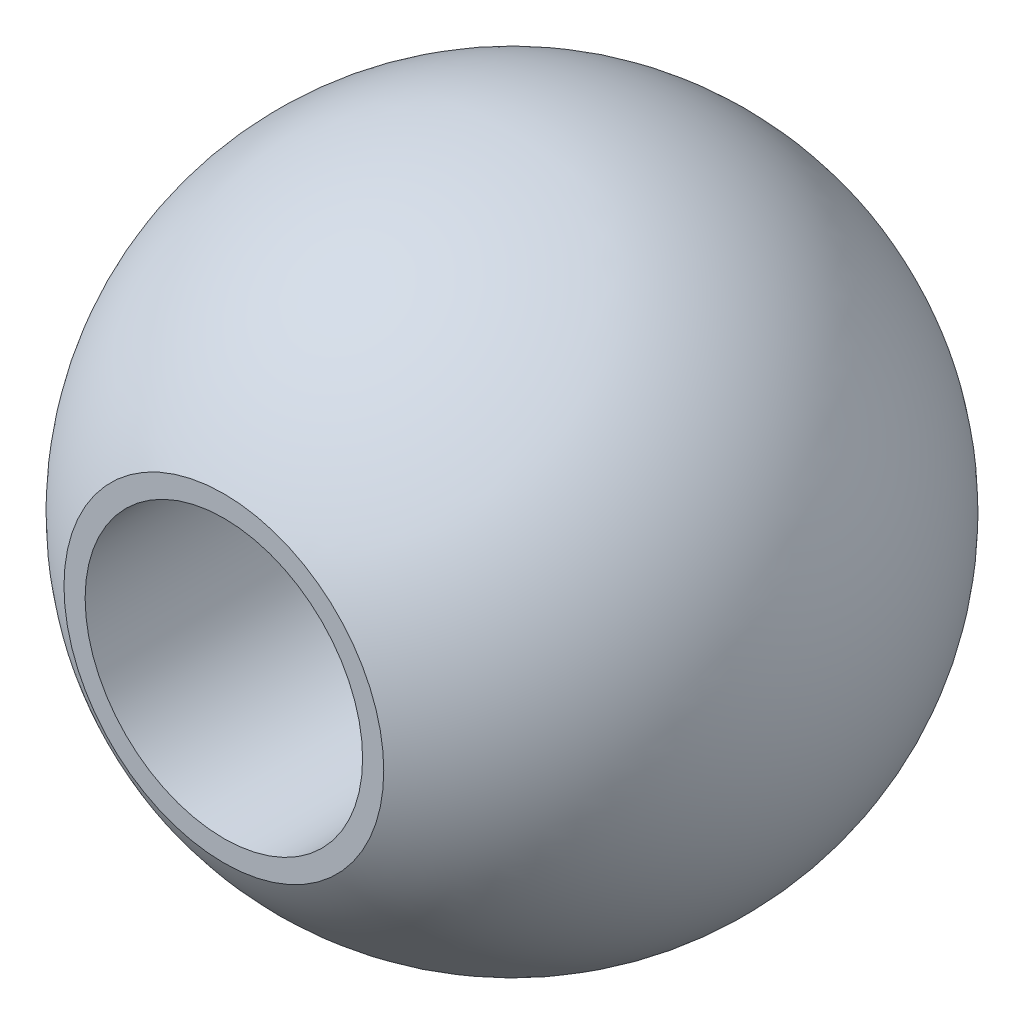
SolidWorks part; units mm, degrees
ref_plane "Front Plane" through (0, 0, 0) normal (0, 0, 1) x (1, 0, 0)
ref_plane "Top Plane" through (0, 0, 0) normal (0, 1, 0) x (1, 0, 0)
ref_plane "Right Plane" through (0, 0, 0) normal (1, 0, 0) x (0, 0, -1)
sketch "Sketch1" plane through (0, 0, 0) normal (0, 0, 1) x (1, 0, 0)
  line L0 (0, 0) -> (0, 9.5)
  line L1 (0, 0) -> (0, -9.5)
  arc A0 (0, -9.5) -> (0, 9.5) centre (0, 0) cw
  dimension "D1" = 9.5
revolve "Revolve1" add sketch "Sketch1" angle 360 about L0
sketch "Sketch2" plane through (0, 0, 0) normal (0, 0, 1) x (1, 0, 0)
  circle A0 centre (0, 0) radius 4
  dimension "D1" = 8
extrude "Cut-Extrude1" cut sketch "Sketch2" against normal through all both and the other way through all contours A0
sketch "Sketch3" plane through (0, 0, 0) normal (1, 0, 0) x (0, 0, -1)
  line L0 (-8.3065, 4.6099) -> (-8.3065, -4.6099)
  line L1 (0, 10.45) -> (0, -10.45) construction
  line L2 (8.3065, 4.6099) -> (8.3065, -4.6099)
  line L3 (-8.3065, 4.6099) -> (-10.3098, 4.8314)
  line L4 (-10.3098, 4.8314) -> (-10.6333, -4.9823)
  line L5 (-10.6333, -4.9823) -> (-8.3065, -4.6099)
  line L6 (8.3065, -4.6099) -> (13.1999, -3.3863)
  line L7 (13.1999, -3.3863) -> (13.1999, 5.6294)
  line L8 (13.1999, 5.6294) -> (8.3065, 4.6099)
  arc A0 (8.6168, 4) -> (-8.6168, 4) centre (0, 0) ccw construction
  arc A1 (-8.6168, -4) -> (8.6168, -4) centre (0, 0) ccw construction
extrude "Cut-Extrude2" cut sketch "Sketch3" against normal through all both and the other way through all
